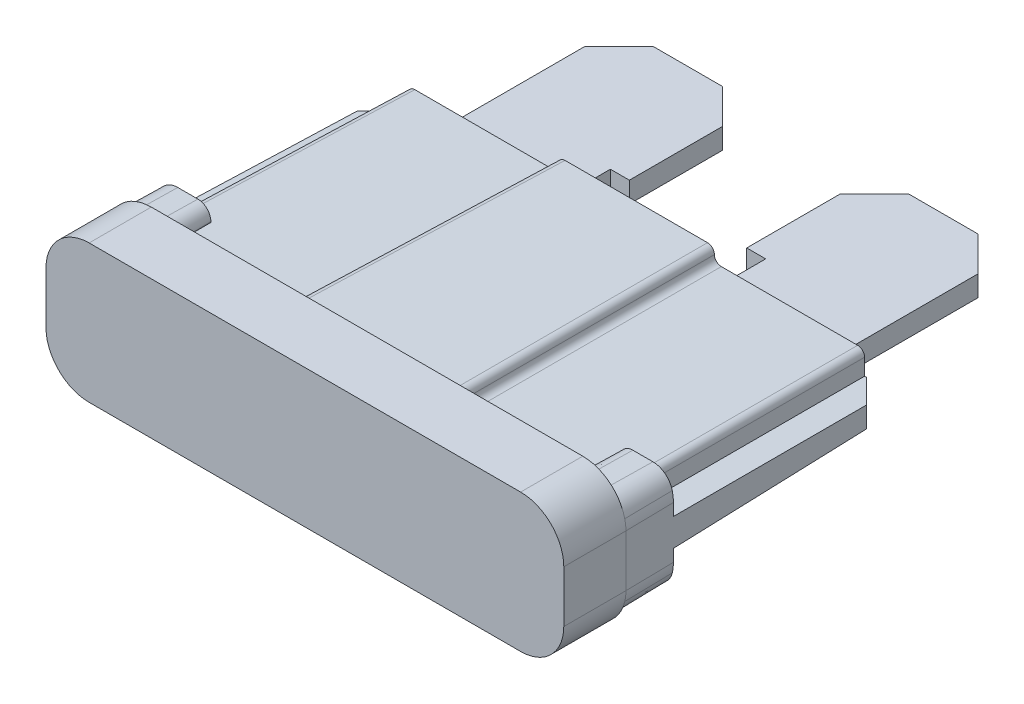
SolidWorks part; units mm, degrees
ref_plane "Plane1" through (0, 0, 0) normal (0, 0, 1) x (1, 0, 0)
ref_plane "Plane2" through (0, 0, 0) normal (0, 1, 0) x (1, 0, 0)
ref_plane "Plane3" through (0, 0, 0) normal (1, 0, 0) x (0, 0, -1)
sketch "Sketch1" plane through (0, 0, 0) normal (0, 0, 1) x (1, 0, 0)
  line L0 (0, 0) -> (0, 6.3939) construction
  line L1 (-9.525, 2.54) -> (9.525, 2.54)
  line L2 (-9.525, 2.54) -> (-9.525, -2.54)
  line L3 (-9.525, -2.54) -> (9.525, -2.54)
  line L4 (9.525, 2.54) -> (9.525, -2.54)
  line L5 (0, 0) -> (8.7866, 0) construction
  point P8 (0, 2.54)
  point P10 (9.525, 0)
  dimension "D1" = 19.05
  dimension "D2" = 5.08
extrude "Base-Extrude" add sketch "Sketch1" against normal blind 2.286
fillet "Fillet1" radius 1.5875 4 edges at (-9.525, 2.54, -1.143) (9.525, 2.54, -1.143) (9.525, -2.54, -1.143) (-9.525, -2.54, -1.143)
sketch "Sketch2" plane through (0, 0, -2.286) normal (0, 0, -1) x (-1, 0, 0)
  line L0 (0, 0) -> (10.4993, 0) construction
  line L1 (-3.048, 1.905) -> (3.048, 1.905)
  line L2 (-3.048, 1.905) -> (-3.048, 1.397)
  line L3 (-3.048, -1.905) -> (3.048, -1.905)
  line L4 (3.048, 1.905) -> (3.048, 1.397)
  line L5 (-8.5725, 1.397) -> (-3.048, 1.397)
  line L6 (-8.5725, 1.397) -> (-8.5725, -1.397)
  line L7 (-8.5725, -1.397) -> (-3.048, -1.397)
  line L8 (8.5725, 1.397) -> (8.5725, -1.397)
  line L9 (0, 0) -> (0, 4.7084) construction
  line L10 (3.048, -1.397) -> (3.048, -1.905)
  line L11 (3.048, 1.397) -> (8.5725, 1.397)
  line L12 (-3.048, -1.397) -> (-3.048, -1.905)
  line L13 (3.048, -1.397) -> (8.5725, -1.397)
  point P13 (0, 1.905)
  point P18 (8.5725, 0)
  dimension "D1" = 3.81
  dimension "D2" = 6.096
  dimension "D3" = 17.145
  dimension "D4" = 2.794
extrude "Boss-Extrude3" add sketch "Sketch2" along normal offset from surface 12.192 draft 1
fillet "Fillet4" radius 0.254 12 edges at (-2.9615, 1.8185, -7.239) (-2.9615, 1.3105, -7.239) (-8.486, 1.3105, -7.239) (-8.486, -1.3105, -7.239) (-2.9615, -1.3105, -7.239) (-2.9615, -1.8185, -7.239) (2.9615, -1.8185, -7.239) (2.9615, -1.3105, -7.239) (8.486, -1.3105, -7.239) (8.486, 1.3105, -7.239) (2.9615, 1.3105, -7.239) (2.9615, 1.8185, -7.239)
sketch "Sketch3" plane through (0, 0, -2.286) normal (0, 0, -1) x (-1, 0, 0)
  line L0 (-9.525, -0.9525) -> (-9.525, 0.9525) construction
  line L1 (-9.525, -0.9525) -> (-9.525, 0.9525)
  line L2 (-8.7407, 1.905) -> (-8.001, 1.905)
  line L3 (-7.493, 1.397) -> (-7.493, -1.397)
  line L4 (-8.7407, -1.905) -> (-8.001, -1.905)
  line L5 (0, 0) -> (-12.6347, 0) construction
  line L6 (0, 0) -> (0, 9.8799) construction
  line L7 (8.7407, -1.905) -> (8.001, -1.905)
  line L8 (7.493, 1.397) -> (7.493, -1.397)
  line L9 (8.7407, 1.905) -> (8.001, 1.905)
  line L10 (9.525, -0.9525) -> (9.525, 0.9525)
  arc A0 (-9.525, -0.9525) -> (-7.9375, -2.54) centre (-7.9375, -0.9525) ccw construction
  arc A1 (-7.9375, 2.54) -> (-9.525, 0.9525) centre (-7.9375, 0.9525) ccw construction
  arc A2 (-8.001, -1.905) -> (-7.493, -1.397) centre (-8.001, -1.397) ccw
  arc A3 (-8.001, 1.905) -> (-7.493, 1.397) centre (-8.001, 1.397) cw
  arc A6 (-9.525, -0.9525) -> (-9.4822, -1.3188) centre (-7.9375, -0.9525) ccw
  arc A7 (-9.4822, 1.3188) -> (-9.525, 0.9525) centre (-7.9375, 0.9525) ccw
  arc A8 (-9.4822, 1.3188) -> (-8.7407, 1.905) centre (-8.7407, 1.143) cw
  arc A9 (-8.7407, -1.905) -> (-9.4822, -1.3188) centre (-8.7407, -1.143) cw
  arc A10 (8.7407, -1.905) -> (9.4822, -1.3188) centre (8.7407, -1.143) ccw
  arc A11 (9.4822, 1.3188) -> (8.7407, 1.905) centre (8.7407, 1.143) ccw
  arc A12 (9.4822, 1.3188) -> (9.525, 0.9525) centre (7.9375, 0.9525) cw
  arc A13 (9.525, -0.9525) -> (9.4822, -1.3188) centre (7.9375, -0.9525) cw
  arc A14 (8.001, 1.905) -> (7.493, 1.397) centre (8.001, 1.397) ccw
  arc A15 (8.001, -1.905) -> (7.493, -1.397) centre (8.001, -1.397) cw
  point P22 (-7.493, 0)
  dimension "D1" = 0.762
  dimension "D4" = 0.508
  dimension "D2" = 3.81
  dimension "D3" = 2.032
extrude "Boss-Extrude4" add sketch "Sketch3" along normal blind 1.778 draft 1
sketch "Sketch5" plane through (0, 0, -4.064) normal (0, 0, -1) x (-1, 0, 0)
  line L0 (-9.494, 0.9525) -> (-9.494, -0.9525) construction
  line L1 (-9.494, 0.508) -> (-9.494, -0.508)
  line L2 (-9.494, 0.508) -> (-7.6322, 0.508)
  line L3 (-7.6322, 0.508) -> (-7.6322, -0.508)
  line L4 (-7.6322, -0.508) -> (-9.494, -0.508)
  line L5 (0, 0) -> (-10.205, 0) construction
  line L6 (0, 0) -> (0, 4.9575) construction
  line L7 (7.6322, -0.508) -> (9.494, -0.508)
  line L8 (7.6322, 0.508) -> (7.6322, -0.508)
  line L9 (9.494, 0.508) -> (7.6322, 0.508)
  line L10 (9.494, 0.508) -> (9.494, -0.508)
  point P9 (-9.494, 0)
  dimension "D1" = 1.016
extrude "Boss-Extrude6" add sketch "Sketch5" along normal up to surface (8.128 mm away) draft 1
chamfer "Chamfer1" distance 0.889 angle 45 2 edges at (9.3521, 0, -12.192) (-9.3521, 0, -12.192)
sketch "Sketch6" plane through (0, 0, 0) normal (0, 1, 0) x (1, 0, 0)
  line L0 (-7.239, 12.192) -> (-7.239, 17.526)
  line L1 (-3.1291, 12.192) -> (-8.1456, 12.192) construction
  line L2 (-7.239, 17.526) -> (-5.969, 18.796)
  line L3 (-5.969, 18.796) -> (-3.429, 18.796)
  line L4 (-3.429, 18.796) -> (-2.159, 17.526)
  line L5 (-2.159, 17.526) -> (-2.159, 14.097)
  line L6 (-2.159, 14.097) -> (-2.8575, 14.097)
  line L7 (-2.8575, 14.097) -> (-2.8575, 12.192)
  line L8 (0, 0) -> (0, 22.2544) construction
  line L9 (-2.8575, 12.192) -> (-7.239, 12.192)
  line L10 (7.9375, 0) -> (-7.9375, 0) construction
  line L11 (2.6211, 12.192) -> (-2.6211, 12.192) construction
  line L12 (2.8575, 12.192) -> (7.239, 12.192)
  line L13 (2.8575, 14.097) -> (2.8575, 12.192)
  line L14 (2.159, 14.097) -> (2.8575, 14.097)
  line L15 (2.159, 17.526) -> (2.159, 14.097)
  line L16 (3.429, 18.796) -> (2.159, 17.526)
  line L17 (5.969, 18.796) -> (3.429, 18.796)
  line L18 (7.239, 17.526) -> (5.969, 18.796)
  line L19 (7.239, 12.192) -> (7.239, 17.526)
  dimension "D1" = 14.478
  dimension "D2" = 18.796
  dimension "D3" = 45
  dimension "D4" = 1.27
  dimension "D5" = 5.08
  dimension "D6" = 5.715
  dimension "D7" = 1.905
extrude "Blades" add sketch "Sketch6" along normal mid plane 0.762
sketch "Skizze1" plane through (0, -1.9443, -0.0339) normal (0, -0.9998, -0.0175) x (1, 0, 0)
  line L1 (0, 0) -> (0, -5.2728) construction
  line L2 (-1.9915, -5.2728) -> (1.4731, -5.2728) construction
  text T0 "15A" font "Century Gothic" height 1.5
extrude "Schnitt-Linear austragen1" cut sketch "Skizze1" against normal blind 0.05
